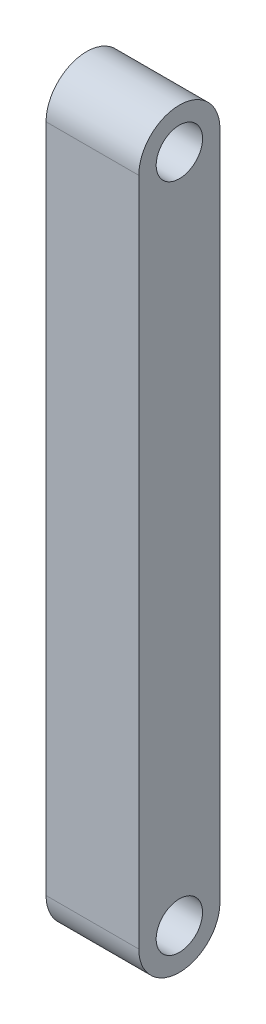
SolidWorks part; units mm, degrees
ref_plane "Front Plane" through (0, 0, 0) normal (0, 0, 1) x (1, 0, 0)
ref_plane "Top Plane" through (0, 0, 0) normal (0, 1, 0) x (1, 0, 0)
ref_plane "Right Plane" through (0, 0, 0) normal (1, 0, 0) x (0, 0, -1)
sketch "Sketch1" plane through (0, 0, 0) normal (1, 0, 0) x (0, 0, -1)
  line L0 (0, 0) -> (0, -57.8) construction
  line L1 (-3.5, 0) -> (-3.5, -57.8)
  line L2 (3.5, 0) -> (3.5, -57.8)
  circle A0 centre (0, 0) radius 2
  circle A1 centre (0, 0) radius 3.5
  circle A2 centre (0, -57.8) radius 2
  circle A3 centre (0, -57.8) radius 3.5
  dimension "D1" = 4
  dimension "D2" = 7
  dimension "D3" = 57.8
extrude "Boss-Extrude1" add sketch "Sketch1" along normal blind 8
